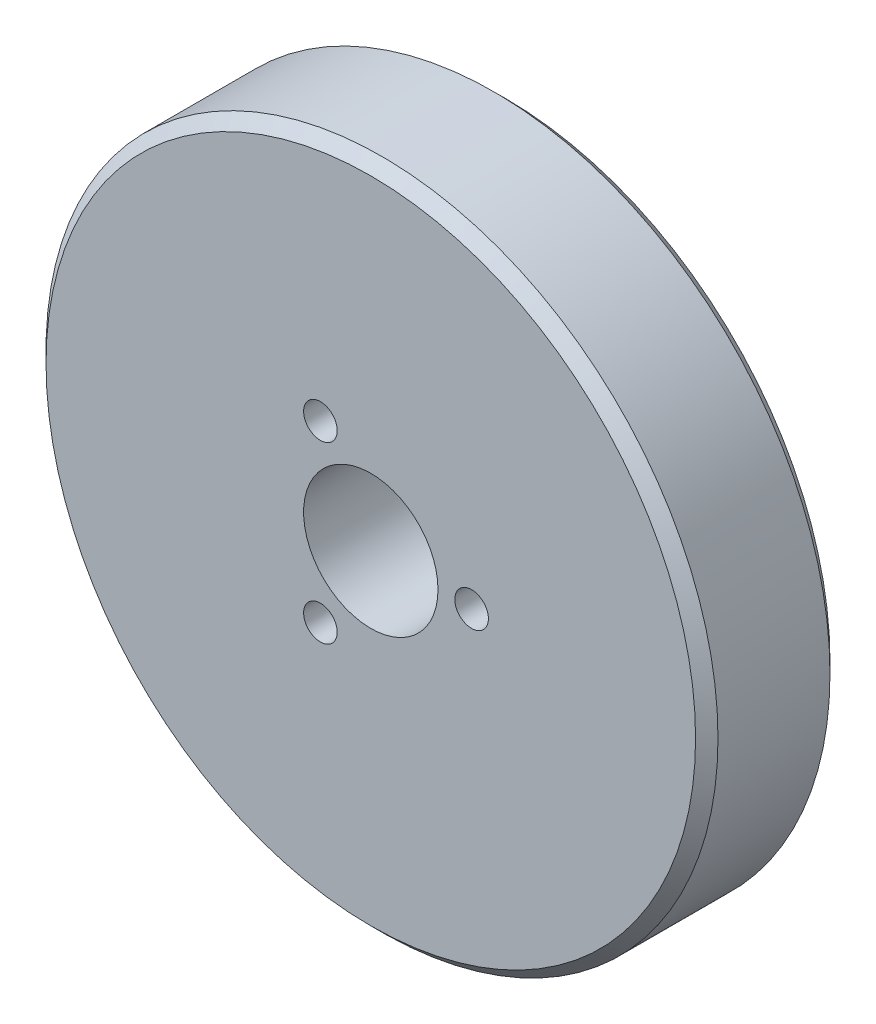
SolidWorks part; units mm, degrees
ref_plane "Front Plane" through (0, 0, 0) normal (0, 0, 1) x (1, 0, 0)
ref_plane "Top Plane" through (0, 0, 0) normal (0, 1, 0) x (1, 0, 0)
ref_plane "Right Plane" through (0, 0, 0) normal (1, 0, 0) x (0, 0, -1)
sketch "Sketch1" plane through (0, 0, 0) normal (0, 0, 1) x (1, 0, 0)
  circle A0 centre (0, 0) radius 30
  circle A1 centre (0, 0) radius 6
  circle A3 centre (9, 0) radius 1.5
  circle A4 centre (-4.5, -7.7942) radius 1.5
  circle A5 centre (-4.5, 7.7942) radius 1.5
  point P14 (0, 0)
  dimension "D1" = 60
  dimension "D2" = 12
  dimension "D4" = 3
  dimension "D5" = 3
extrude "Boss-Extrude1" add sketch "Sketch1" along normal blind 12
chamfer "Chamfer1" distance 1 angle 45 2 edges at (30, 0, 0) (30, 0, 12)
